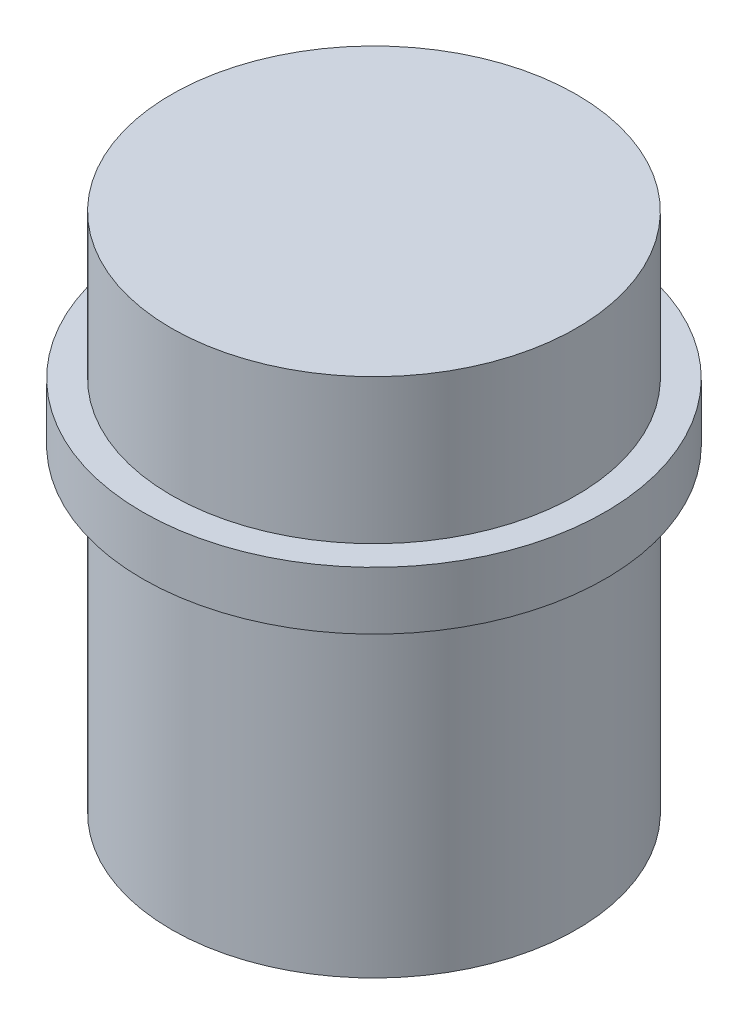
SolidWorks part; units mm, degrees
ref_plane "Front Plane" through (0, 0, 0) normal (0, 0, 1) x (1, 0, 0)
ref_plane "Top Plane" through (0, 0, 0) normal (0, 1, 0) x (1, 0, 0)
ref_plane "Right Plane" through (0, 0, 0) normal (1, 0, 0) x (0, 0, -1)
sketch "Sketch1" plane through (0, 0, 0) normal (0, 1, 0) x (1, 0, 0)
  circle A0 centre (0, 0) radius 8
  dimension "D1" = 16
extrude "Boss-Extrude1" add sketch "Sketch1" along normal blind 2
sketch "Sketch2" plane through (0, 2, 0) normal (0, 1, 0) x (1, 0, 0)
  circle A0 centre (0, 0) radius 7
  dimension "D1" = 14
extrude "Boss-Extrude2" add sketch "Sketch2" along normal blind 5 and the other way blind 13
sketch "Sketch4" plane through (0, -11, 0) normal (0, -1, 0) x (1, 0, 0)
  circle A0 centre (0, 0) radius 5
  dimension "D1" = 10
extrude "Cut-Extrude2" cut sketch "Sketch4" against normal blind 2
